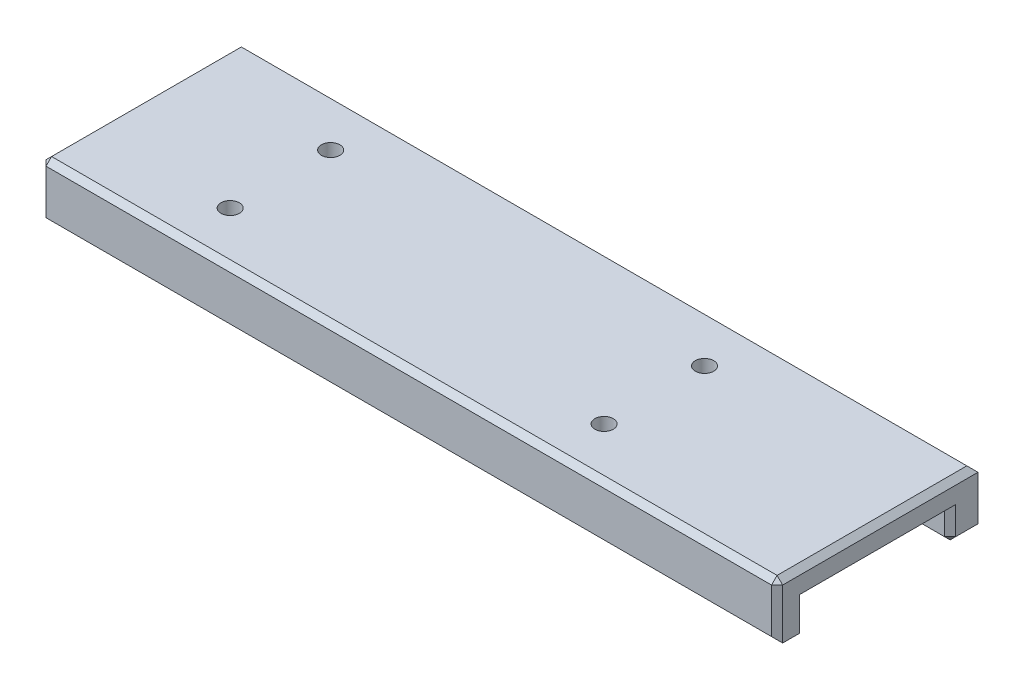
SolidWorks part; units mm, degrees
material "ABS"
ref_plane "Front Plane" through (0, 0, 0) normal (0, 0, 1) x (1, 0, 0)
ref_plane "Top Plane" through (0, 0, 0) normal (0, 1, 0) x (1, 0, 0)
ref_plane "Right Plane" through (0, 0, 0) normal (1, 0, 0) x (0, 0, -1)
sketch "Sketch1" plane through (0, 0, 0) normal (0, 1, 0) x (1, 0, 0)
  line L1 (-66, -18) -> (66, -18)
  line L2 (-66, -18) -> (-66, 18)
  line L3 (-66, 18) -> (66, 18)
  line L4 (66, -18) -> (66, 18)
  line L5 (-66, -18) -> (66, 18) construction
  line L6 (-66, 18) -> (66, -18) construction
  point P0 (0, 0)
  dimension "D1" = 132
  dimension "D2" = 36
extrude "Boss-Extrude1" add sketch "Sketch1" along normal mid plane 10
sketch "Sketch2" plane through (0, 0, 0) normal (1, 0, 0) x (0, 0, -1)
  line L0 (-13, 0) -> (13, 0)
  line L1 (13, 0) -> (13, -5)
  line L2 (-18, -5) -> (18, -5) construction
  line L3 (13, -5) -> (-13, -5)
  line L4 (-13, -5) -> (-13, 0)
  line L5 (-18, 5) -> (-18, -5) construction
  dimension "D1" = 5
extrude "Cut-Extrude1" cut sketch "Sketch2" against normal through all both and the other way through all
chamfer "Chamfer1" distance 1 angle 45 17 edges at (-66, -2.5, 13) (-66, -5, -15.5) (-66, 0, 0) (-66, -2.5, -13) (0, -5, 13) (66, -5, -15.5) (66, -2.5, -13) (66, 0, 0) (66, -2.5, 13) (0, -5, 18) (66, 0, 18) (66, 5, 0) (0, 5, -18) (-66, 5, 0) (0, 5, 18) (-66, 0, 18) (0, -5, -13)
hole_wizard "Tap Drill for M4x0.7 Tap1" positions "Sketch3" profile "Sketch4" hole size "M4x0.7" standard "ANSI Metric"
sketch "Sketch3" plane through (-96, 5, 18) normal (0, 1, 0) x (1, 0, 0)
  line L0 (55, 13.5) -> (55, 9) construction
  line L4 (122, 13.7857) -> (122, 9) construction
  point P0 (55, 27)
  point P3 (122, 27)
  point P8 (55, 9)
  point P15 (122, 9)
sketch "Sketch4" plane through (-41, 5, -9) normal (1, 0, 0) x (0, 0, 1)
  line L0 (0, 0) -> (0, 14.9914)
  line L1 (0, 14.9914) -> (1.65, 14)
  line L2 (1.65, 14) -> (1.65, 0)
  line L3 (1.65, 0) -> (0, 0)
  line L4 (0, 14.9914) -> (-1.65, 14) construction
  line L5 (0, -6.35) -> (0, 107.95) construction
  dimension "Hole Dia." = 3.3
  dimension "Hole Depth" = 14
  dimension "Drill Angle" = 118
